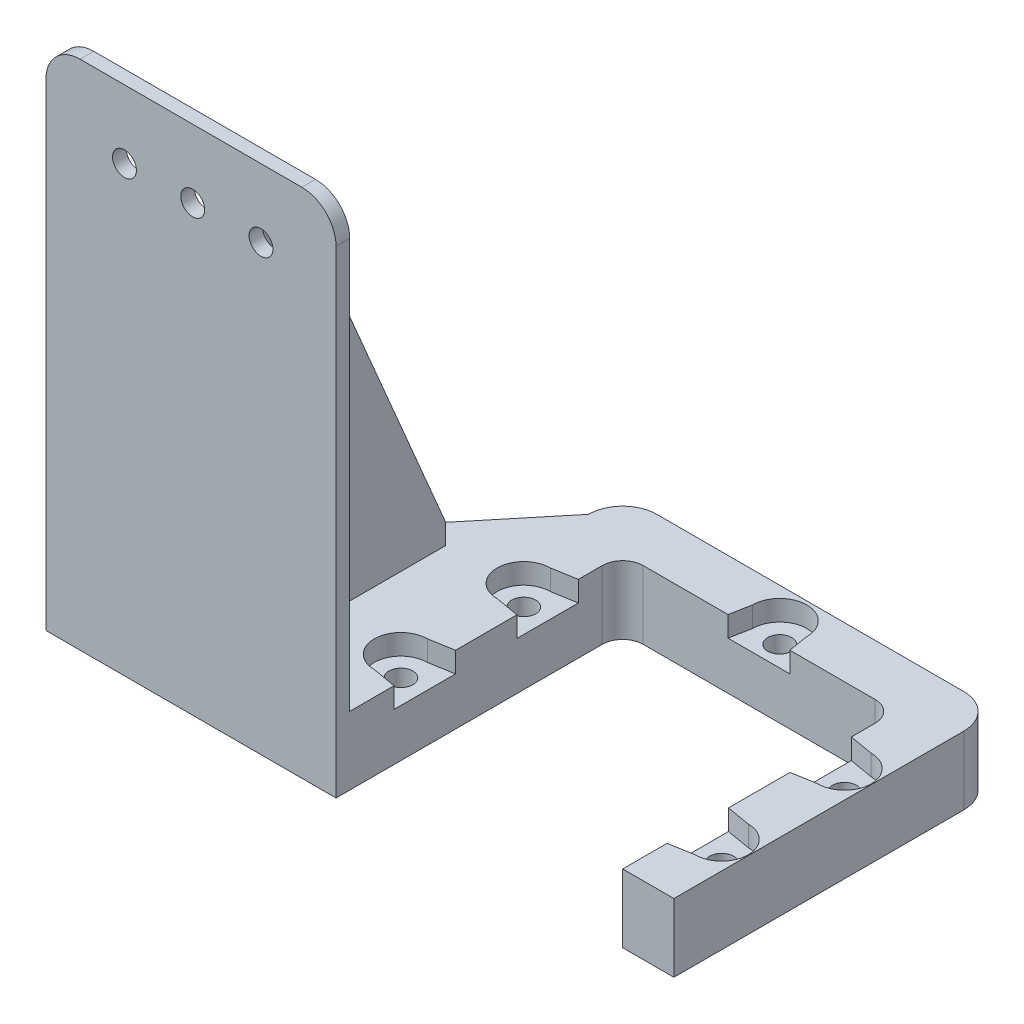
SolidWorks part; units mm, degrees
ref_plane "Front Plane" through (0, 0, 0) normal (0, 0, 1) x (1, 0, 0)
ref_plane "Top Plane" through (0, 0, 0) normal (0, 1, 0) x (1, 0, 0)
ref_plane "Right Plane" through (0, 0, 0) normal (1, 0, 0) x (0, 0, -1)
sketch "Sketch1" plane through (0, 0, 0) normal (0, 1, 0) x (1, 0, 0)
  line L0 (-20, -20) -> (-27.5, -20)
  line L1 (-17, 20) -> (17, 20)
  line L2 (-20, 17) -> (-20, -20)
  line L4 (20, 17) -> (20, -20)
  line L5 (-20, 20) -> (20, -20) construction
  line L6 (-20, -20) -> (20, 20) construction
  line L7 (-22.5, 27.5) -> (22.5, 27.5)
  line L8 (-27.5, 22.5) -> (-27.5, -20)
  line L10 (27.5, 22.5) -> (27.5, -20)
  line L11 (-27.5, 27.5) -> (27.5, -27.5) construction
  line L12 (-27.5, -27.5) -> (27.5, 27.5) construction
  line L13 (20, -20) -> (27.5, -20)
  line L14 (-20, -20) -> (20, -20) construction
  arc A0 (17, 20) -> (20, 17) centre (17, 17) cw
  arc A1 (-17, 20) -> (-20, 17) centre (-17, 17) ccw
  arc A2 (22.5, 27.5) -> (27.5, 22.5) centre (22.5, 22.5) cw
  arc A3 (-22.5, 27.5) -> (-27.5, 22.5) centre (-22.5, 22.5) ccw
  point P0 (0, 0)
  point P12 (0, 0)
  dimension "D3" = 3
  dimension "D6" = 5
  dimension "D1" = 40
  dimension "D2" = 40
  dimension "D4" = 55
  dimension "D5" = 55
  dimension "D9" = 7.5
extrude "Boss-Extrude1" add sketch "Sketch1" along normal blind 10
sketch "Sketch2" plane through (0, 10, 0) normal (0, 1, 0) x (1, 0, 0)
  line L0 (-23.5, -9) -> (23.5, -9) construction
  line L1 (0, -9) -> (0, -20) construction
  line L4 (-20, -20) -> (20, -20) construction
  line L5 (0, 20) -> (0, 23) construction
  line L6 (-17, 20) -> (17, 20) construction
  line L7 (-23.5, 9) -> (23.5, 9) construction
  line L8 (0, 9) -> (0, 20) construction
  circle A0 centre (-23.5, -9) radius 1.75
  circle A1 centre (23.5, -9) radius 1.75
  circle A2 centre (0, 23) radius 1.75
  circle A3 centre (-23.5, 9) radius 1.75
  circle A4 centre (23.5, 9) radius 1.75
  dimension "D3" = 3.5
  dimension "D4" = 3.5
  dimension "D6" = 3.5
  dimension "D9" = 3.5
  dimension "D10" = 3.5
  dimension "D1" = 11
  dimension "D2" = 47
  dimension "D5" = 3
  dimension "47" = 47
  dimension "D8" = 11
extrude "Cut-Extrude1" cut sketch "Sketch2" against normal blind 15.5
sketch "Sketch3" plane through (0, 0, 0) normal (0, -1, 0) x (1, 0, 0)
  line L1 (-20.6, 7.3257) -> (-20.6, 10.6743)
  line L2 (-20.6, 10.6743) -> (-23.5, 12.3486)
  line L3 (-23.5, 12.3486) -> (-26.4, 10.6743)
  line L4 (-26.4, 10.6743) -> (-26.4, 7.3257)
  line L5 (-26.4, 7.3257) -> (-23.5, 5.6514)
  line L6 (-23.5, 5.6514) -> (-20.6, 7.3257)
  line L7 (23.4997, 5.6514) -> (26.3998, 7.3254)
  line L8 (26.3998, 7.3254) -> (26.4002, 10.674)
  line L9 (26.4002, 10.674) -> (23.5003, 12.3486)
  line L10 (23.5003, 12.3486) -> (20.6002, 10.6746)
  line L11 (20.6002, 10.6746) -> (20.5998, 7.326)
  line L12 (20.5998, 7.326) -> (23.4997, 5.6514)
  line L13 (3.3486, -23) -> (1.6743, -20.1)
  line L14 (1.6743, -20.1) -> (-1.6743, -20.1)
  line L15 (-1.6743, -20.1) -> (-3.3486, -23)
  line L16 (-3.3486, -23) -> (-1.6743, -25.9)
  line L17 (-1.6743, -25.9) -> (1.6743, -25.9)
  line L18 (1.6743, -25.9) -> (3.3486, -23)
  line L19 (-23.4997, -5.6514) -> (-26.3998, -7.3254)
  line L20 (-26.3998, -7.3254) -> (-26.4002, -10.674)
  line L21 (-26.4002, -10.674) -> (-23.5003, -12.3486)
  line L22 (-23.5003, -12.3486) -> (-20.6002, -10.6746)
  line L23 (-20.6002, -10.6746) -> (-20.5998, -7.326)
  line L24 (-20.5998, -7.326) -> (-23.4997, -5.6514)
  line L25 (23.4997, -5.6514) -> (20.5998, -7.326)
  line L26 (20.5998, -7.326) -> (20.6002, -10.6746)
  line L27 (20.6002, -10.6746) -> (23.5003, -12.3486)
  line L28 (23.5003, -12.3486) -> (26.4002, -10.674)
  line L29 (26.4002, -10.674) -> (26.3998, -7.3254)
  line L30 (26.3998, -7.3254) -> (23.4997, -5.6514)
  circle A0 centre (-23.5, 9) radius 2.9 construction
  circle A1 centre (23.5, 9) radius 2.9 construction
  circle A2 centre (0, -23) radius 2.9 construction
  circle A3 centre (-23.5, -9) radius 2.9 construction
  circle A4 centre (23.5, -9) radius 2.9 construction
  dimension "D1" = 5.8
  dimension "D2" = 5.8
  dimension "D3" = 5.8
  dimension "D4" = 5.8
  dimension "D5" = 5.8
extrude "Cut-Extrude2" cut sketch "Sketch3" against normal blind 3
sketch "Sketch8" plane through (0, 10, 0) normal (0, 1, 0) x (1, 0, 0)
  line L0 (-4, 23) -> (-4.5746, 20)
  line L1 (-17, 20) -> (17, 20) construction
  line L2 (-4.5746, 20) -> (4.4783, 20)
  line L3 (4.4783, 20) -> (4, 23)
  line L4 (23.5, 12.9) -> (20, 13.5)
  line L5 (20, 17) -> (20, -20) construction
  line L6 (20, 13.5) -> (20, 4.5)
  line L7 (20, 4.5) -> (23.5, 5.1)
  line L8 (23.5, -5.1) -> (20, -4.5)
  line L9 (20, -4.5) -> (20, -13.5)
  line L10 (20, -13.5) -> (23.5, -12.9)
  line L11 (-23.5, -12.9) -> (-20, -13.5)
  line L12 (-20, -20) -> (-20, 17) construction
  line L13 (-20, -13.5) -> (-20, -4.5)
  line L14 (-20, -4.5) -> (-23.5, -5.1)
  line L15 (-20, -9) -> (-23.5, -9) construction
  line L16 (20, -9) -> (23.5, -9) construction
  line L17 (20, 9) -> (23.5, 9) construction
  line L18 (-0.0481, 20) -> (0, 23) construction
  line L19 (-23.5, 12.9) -> (-20, 13.5)
  line L20 (-20, 13.5) -> (-20, 4.5)
  line L21 (-20, 4.5) -> (-23.5, 5.1)
  line L22 (-23.5, 9) -> (-20, 9) construction
  arc A0 (4, 23) -> (-4, 23) centre (0, 23) ccw
  arc A1 (-23.5, 12.9) -> (-23.5, 5.1) centre (-23.5, 9) ccw
  arc A2 (-23.5, -5.1) -> (-23.5, -12.9) centre (-23.5, -9) ccw
  arc A4 (23.5, -12.9) -> (23.5, -5.1) centre (23.5, -9) ccw
  arc A5 (23.5, 5.1) -> (23.5, 12.9) centre (23.5, 9) ccw
  dimension "D1" = 9
  dimension "D2" = 9
  dimension "D3" = 9
  dimension "D4" = 9
extrude "Cut-Extrude7" cut sketch "Sketch8" against normal blind 3
sketch "Sketch9" plane through (0, 0, 20) normal (0, 0, 1) x (1, 0, 0)
  line L0 (-20, 10) -> (-20, -5)
  line L1 (-20, 10) -> (-45, 10)
  line L2 (-20, -5) -> (-45, -5)
  line L3 (-45, 10) -> (-45, -5)
  dimension "D1" = 25
  dimension "D2" = 15
sketch "Sketch10" plane through (0, 0, 0) normal (0, 1, 0) x (1, 0, 0)
  line L0 (-27.5, 22.5) -> (-62.5, -20)
  line L1 (-62.5, -20) -> (-27.5, -20)
  line L2 (-27.5, -20) -> (-27.5, 22.5)
  dimension "D1" = 35
extrude "Boss-Extrude2" add sketch "Sketch10" along normal blind 10
sketch "Sketch11" plane through (0, 0, 20) normal (0, 0, 1) x (1, 0, 0)
  line L1 (-62.5, 0) -> (-20, 0)
  line L2 (-62.5, 0) -> (-62.5, 75)
  line L3 (-62.5, 75) -> (-20, 75)
  line L4 (-20, 0) -> (-20, 75)
  dimension "D1" = 75
extrude "Boss-Extrude3" add sketch "Sketch11" along normal blind 2
sketch "Sketch12" plane through (0, 10, 0) normal (0, 1, 0) x (1, 0, 0)
  line L0 (-62.5, -20) -> (-20, -20) construction
  line L1 (-37, -20) -> (-34, -20)
  line L2 (-37, -20) -> (-37, 8)
  line L3 (-37, 8) -> (-34, 8)
  line L4 (-34, -20) -> (-34, 8)
  line L5 (-20, -20) -> (-20, -13.5) construction
  dimension "D1" = 17
  dimension "D2" = 3
  dimension "D3" = 28
extrude "Boss-Extrude4" add sketch "Sketch12" along normal blind 62
chamfer "Chamfer1" distance 25 angle 67 1 edges at (-35.5, 72, -8)
fillet "Fillet1" radius 5 2 edges at (-20, 75, 21) (-62.5, 75, 21)
sketch "Sketch13" plane through (0, 0, 20) normal (0, 0, -1) x (-1, 0, 0)
  line L0 (31, 65) -> (41, 65) construction
  line L1 (25, 75) -> (57.5, 75) construction
  line L2 (41, 65) -> (51, 65) construction
  circle A0 centre (31, 65) radius 1.75
  circle A1 centre (41, 65) radius 1.75
  circle A2 centre (51, 65) radius 1.75
  dimension "D3" = 3.5
  dimension "D4" = 3.5
  dimension "D7" = 3.5
  dimension "D1" = 10
  dimension "D2" = 10
  dimension "D5" = 31
  dimension "D6" = 10
extrude "Cut-Extrude8" cut sketch "Sketch13" against normal through all
